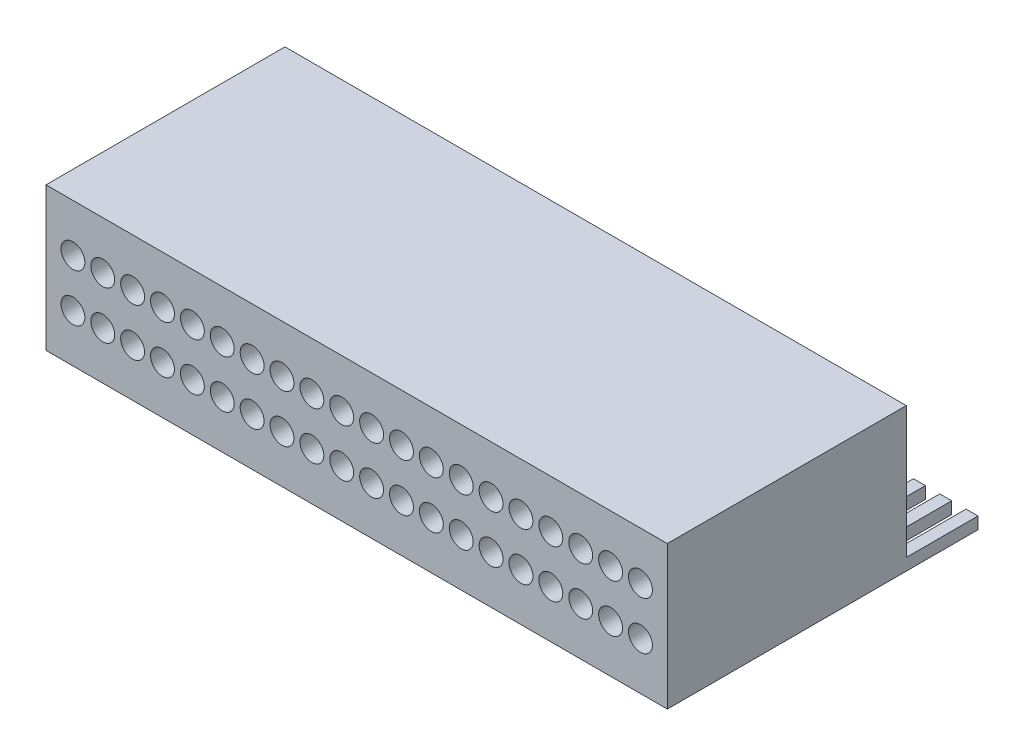
SolidWorks part; units mm, degrees
ref_plane "Front Plane" through (0, 0, 0) normal (0, 0, 1) x (1, 0, 0)
ref_plane "Top Plane" through (0, 0, 0) normal (0, 1, 0) x (1, 0, 0)
ref_plane "Right Plane" through (0, 0, 0) normal (1, 0, 0) x (0, 0, -1)
sketch "Sketch2" plane through (0, 0, 0) normal (0, 0, 1) x (1, 0, 0)
  line L1 (0, 0) -> (26, 0)
  line L2 (0, 0) -> (0, 6)
  line L3 (0, 6) -> (26, 6)
  line L4 (26, 0) -> (26, 6)
  dimension "D1" = 26
  dimension "D2" = 6
extrude "Boss-Extrude1" add sketch "Sketch2" along normal blind 10
sketch "Sketch3" plane through (0, 0, 10) normal (0, 0, 1) x (1, 0, 0)
  line L0 (0, 2) -> (26, 2) construction
  line L1 (0, 6) -> (0, 0) construction
  line L2 (26, 0) -> (26, 6) construction
  line L3 (0, 3) -> (26, 3) construction
  line L4 (26, 6) -> (0, 6) construction
  line L5 (0, 0) -> (26, 0) construction
  line L6 (1.125, 6) -> (1.125, 0) construction
  circle A0 centre (1.125, 2) radius 0.5
  circle A1 centre (2.375, 2) radius 0.5
  circle A2 centre (3.625, 2) radius 0.5
  circle A3 centre (4.875, 2) radius 0.5
  circle A4 centre (6.125, 2) radius 0.5
  circle A5 centre (7.375, 2) radius 0.5
  circle A6 centre (8.625, 2) radius 0.5
  circle A7 centre (9.875, 2) radius 0.5
  circle A8 centre (11.125, 2) radius 0.5
  circle A9 centre (12.375, 2) radius 0.5
  circle A10 centre (13.625, 2) radius 0.5
  circle A11 centre (14.875, 2) radius 0.5
  circle A12 centre (16.125, 2) radius 0.5
  circle A13 centre (17.375, 2) radius 0.5
  circle A14 centre (18.625, 2) radius 0.5
  circle A15 centre (19.875, 2) radius 0.5
  circle A16 centre (21.125, 2) radius 0.5
  circle A17 centre (22.375, 2) radius 0.5
  circle A18 centre (23.625, 2) radius 0.5
  circle A19 centre (24.875, 2) radius 0.5
  dimension "D1" = 1
  dimension "D2" = 2
  dimension "D3" = 1.125
  dimension "D5" = 1.25
  dimension "D4" = 20
extrude "Cut-Extrude1" cut sketch "Sketch3" against normal blind 5
sketch "Sketch4" plane through (0, 0, 0) normal (0, -1, 0) x (-1, 0, 0)
  line L0 (-24.9, 0) -> (-24.9, 3)
  line L1 (-26, 0) -> (-25.5, 0)
  line L2 (-26, 0) -> (-26, 3)
  line L3 (-26, 3) -> (-25.5, 3)
  line L4 (-25.5, 0) -> (-25.5, 3)
  line L5 (-24.9, 3) -> (-24.4, 3)
  line L6 (-24.4, 0) -> (-24.4, 3)
  line L7 (-24.9, 0) -> (-24.4, 0)
  line L8 (-23.8, 0) -> (-23.8, 3)
  line L9 (-23.8, 3) -> (-23.3, 3)
  line L10 (-23.3, 0) -> (-23.3, 3)
  line L11 (-23.8, 0) -> (-23.3, 0)
  line L12 (-22.7, 0) -> (-22.7, 3)
  line L13 (-22.7, 3) -> (-22.2, 3)
  line L14 (-22.2, 0) -> (-22.2, 3)
  line L15 (-22.7, 0) -> (-22.2, 0)
  line L16 (-21.6, 0) -> (-21.6, 3)
  line L17 (-21.6, 3) -> (-21.1, 3)
  line L18 (-21.1, 0) -> (-21.1, 3)
  line L19 (-21.6, 0) -> (-21.1, 0)
  line L20 (-20.5, 0) -> (-20.5, 3)
  line L21 (-20.5, 3) -> (-20, 3)
  line L22 (-20, 0) -> (-20, 3)
  line L23 (-20.5, 0) -> (-20, 0)
  line L24 (-19.4, 0) -> (-19.4, 3)
  line L25 (-19.4, 3) -> (-18.9, 3)
  line L26 (-18.9, 0) -> (-18.9, 3)
  line L27 (-19.4, 0) -> (-18.9, 0)
  line L28 (-18.3, 0) -> (-18.3, 3)
  line L29 (-18.3, 3) -> (-17.8, 3)
  line L30 (-17.8, 0) -> (-17.8, 3)
  line L31 (-18.3, 0) -> (-17.8, 0)
  line L32 (-17.2, 0) -> (-17.2, 3)
  line L33 (-17.2, 3) -> (-16.7, 3)
  line L34 (-16.7, 0) -> (-16.7, 3)
  line L35 (-17.2, 0) -> (-16.7, 0)
  line L36 (-16.1, 0) -> (-16.1, 3)
  line L37 (-16.1, 3) -> (-15.6, 3)
  line L38 (-15.6, 0) -> (-15.6, 3)
  line L39 (-16.1, 0) -> (-15.6, 0)
  line L40 (-15, 0) -> (-15, 3)
  line L41 (-15, 3) -> (-14.5, 3)
  line L42 (-14.5, 0) -> (-14.5, 3)
  line L43 (-15, 0) -> (-14.5, 0)
  line L44 (-13.9, 0) -> (-13.9, 3)
  line L45 (-13.9, 3) -> (-13.4, 3)
  line L46 (-13.4, 0) -> (-13.4, 3)
  line L47 (-13.9, 0) -> (-13.4, 0)
  line L48 (-12.8, 0) -> (-12.8, 3)
  line L49 (-12.8, 3) -> (-12.3, 3)
  line L50 (-12.3, 0) -> (-12.3, 3)
  line L51 (-12.8, 0) -> (-12.3, 0)
  line L52 (-11.7, 0) -> (-11.7, 3)
  line L53 (-11.7, 3) -> (-11.2, 3)
  line L54 (-11.2, 0) -> (-11.2, 3)
  line L55 (-11.7, 0) -> (-11.2, 0)
  line L56 (-10.6, 0) -> (-10.6, 3)
  line L57 (-10.6, 3) -> (-10.1, 3)
  line L58 (-10.1, 0) -> (-10.1, 3)
  line L59 (-10.6, 0) -> (-10.1, 0)
  line L60 (-9.5, 0) -> (-9.5, 3)
  line L61 (-9.5, 3) -> (-9, 3)
  line L62 (-9, 0) -> (-9, 3)
  line L63 (-9.5, 0) -> (-9, 0)
  line L64 (-8.4, 0) -> (-8.4, 3)
  line L65 (-8.4, 3) -> (-7.9, 3)
  line L66 (-7.9, 0) -> (-7.9, 3)
  line L67 (-8.4, 0) -> (-7.9, 0)
  line L68 (-7.3, 0) -> (-7.3, 3)
  line L69 (-7.3, 3) -> (-6.8, 3)
  line L70 (-6.8, 0) -> (-6.8, 3)
  line L71 (-7.3, 0) -> (-6.8, 0)
  line L72 (-6.2, 0) -> (-6.2, 3)
  line L73 (-6.2, 3) -> (-5.7, 3)
  line L74 (-5.7, 0) -> (-5.7, 3)
  line L75 (-6.2, 0) -> (-5.7, 0)
  line L76 (-5.1, 0) -> (-5.1, 3)
  line L77 (-5.1, 3) -> (-4.6, 3)
  line L78 (-4.6, 0) -> (-4.6, 3)
  line L79 (-5.1, 0) -> (-4.6, 0)
  line L80 (-4, 0) -> (-4, 3)
  line L81 (-4, 3) -> (-3.5, 3)
  line L82 (-3.5, 0) -> (-3.5, 3)
  line L83 (-4, 0) -> (-3.5, 0)
  line L84 (-2.9, 0) -> (-2.9, 3)
  line L85 (-2.9, 3) -> (-2.4, 3)
  line L86 (-2.4, 0) -> (-2.4, 3)
  line L87 (-2.9, 0) -> (-2.4, 0)
  line L88 (-1.8, 0) -> (-1.8, 3)
  line L89 (-1.8, 3) -> (-1.3, 3)
  line L90 (-1.3, 0) -> (-1.3, 3)
  line L91 (-1.8, 0) -> (-1.3, 0)
  line L92 (-0.7, 0) -> (-0.7, 3)
  line L93 (-0.7, 3) -> (-0.2, 3)
  line L94 (-0.2, 0) -> (-0.2, 3)
  line L95 (-0.7, 0) -> (-0.2, 0)
  line L96 (-26, 0) -> (-24.9, 0) construction
  dimension "D1" = 3
  dimension "D2" = 0.5
  dimension "D4" = 1.1
  dimension "D3" = 24
extrude "Boss-Extrude2" add sketch "Sketch4" against normal blind 0.5
ref_plane "Plane1" through (0, 3, 0) normal (0, -1, 0) x (-1, 0, 0)
mirror "Mirror1" about plane through (0, 3, 0) normal (0, -1, 0) of "Cut-Extrude1"
sketch "Sketch5" plane through (0, 0, 10) normal (0, 0, 1) x (1, 0, 0)
  point P0 (1.125, 4)
  point P1 (2.375, 4)
  point P3 (3.625, 4)
  point P5 (4.875, 4)
  point P7 (6.125, 4)
  point P9 (7.375, 4)
  point P11 (8.625, 4)
  point P13 (9.875, 4)
  point P15 (11.125, 4)
  point P17 (12.375, 4)
  point P19 (13.625, 4)
  point P21 (14.875, 4)
  point P23 (16.125, 4)
  point P25 (17.375, 4)
  point P27 (18.625, 4)
  point P29 (19.875, 4)
  point P31 (21.125, 4)
  point P33 (22.375, 4)
  point P35 (23.625, 4)
  point P37 (24.875, 4)
  point P39 (24.875, 2)
  point P41 (23.625, 2)
  point P43 (22.375, 2)
  point P45 (21.125, 2)
  point P47 (19.875, 2)
  point P49 (18.625, 2)
  point P51 (17.375, 2)
  point P53 (16.125, 2)
  point P55 (14.875, 2)
  point P57 (13.625, 2)
  point P59 (12.375, 2)
  point P61 (11.125, 2)
  point P63 (9.875, 2)
  point P65 (8.625, 2)
  point P67 (7.375, 2)
  point P69 (6.125, 2)
  point P71 (4.875, 2)
  point P73 (3.625, 2)
  point P75 (2.375, 2)
  point P77 (1.125, 2)
